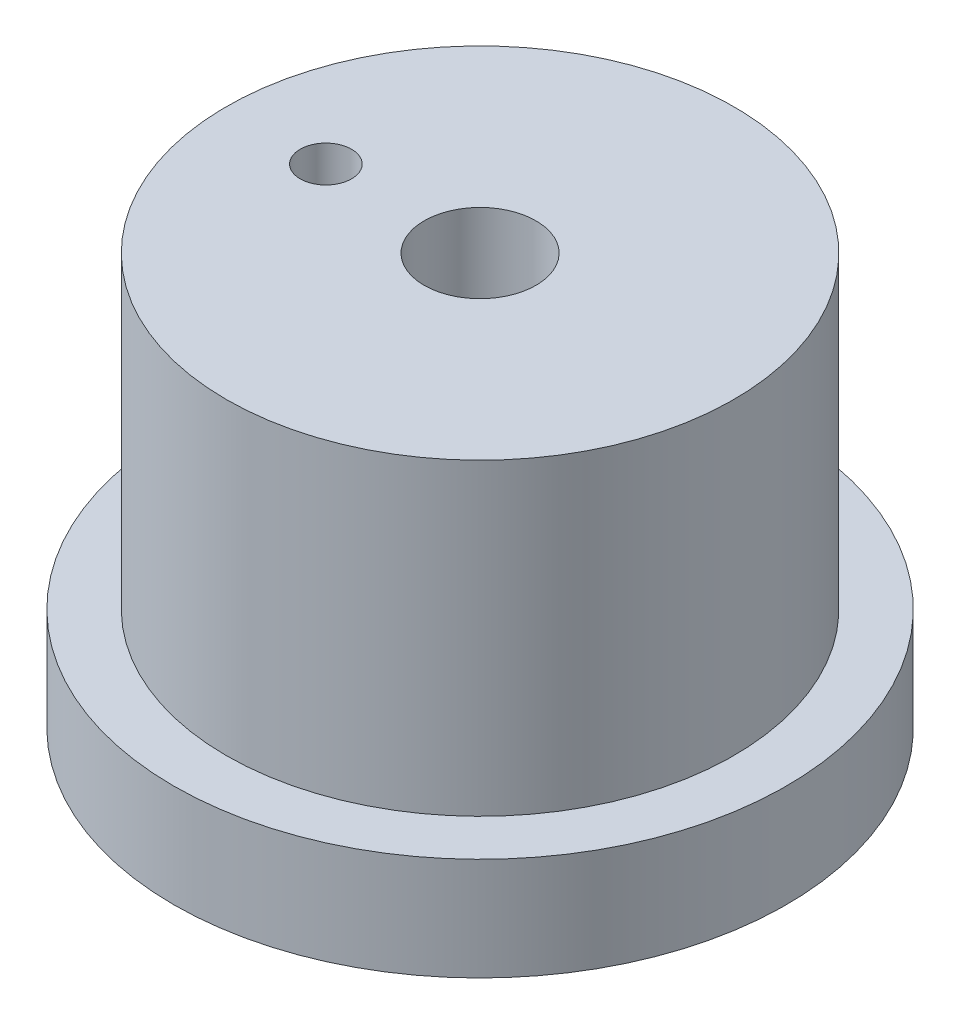
SolidWorks part; units mm, degrees
material "Stainless Steel"
ref_plane "Front Plane" through (0, 0, 0) normal (0, 0, 1) x (1, 0, 0)
ref_plane "Top Plane" through (0, 0, 0) normal (0, 1, 0) x (1, 0, 0)
ref_plane "Right Plane" through (0, 0, 0) normal (1, 0, 0) x (0, 0, -1)
sketch "Sketch1" plane through (0, 0, 0) normal (0, 1, 0) x (1, 0, 0)
  circle A0 centre (0, 0) radius 9.4615
  dimension "D1" = 18.923
extrude "Extrude1" add sketch "Sketch1" along normal blind 3.175
sketch "Sketch2" plane through (0, 3.175, 0) normal (0, 1, 0) x (1, 0, 0)
  circle A0 centre (0, 0) radius 7.8359
  dimension "D1" = 15.6718
extrude "Extrude2" add sketch "Sketch2" along normal blind 9.525
sketch "Sketch3" plane through (0, 0, 0) normal (0, -1, 0) x (1, 0, 0)
  circle A0 centre (0, 0) radius 7.4295
  dimension "D1" = 14.859
extrude "Cut-Extrude1" cut sketch "Sketch3" against normal blind 0.635
sketch "Sketch4" plane through (0, 12.7, 0) normal (0, 1, 0) x (1, 0, 0)
  line L0 (-7.8359, 0) -> (7.8359, 0) construction
  line L1 (0, 7.8359) -> (0, -7.8359) construction
  circle A0 centre (0, 0) radius 7.8359 construction
  circle A1 centre (0, 0) radius 7.8359 construction
hole_wizard "#8-32 Tapped Hole1" positions "3DSketch1" profile "Sketch5" tap size "#8-32" standard "ANSI Inch" end condition up to next
sketch3d "3DSketch1"
  line L0 (-7.8359, 12.7, 0) -> (7.8359, 12.7, 0) construction
  line L1 (0, 12.7, -7.8359) -> (0, 12.7, 7.8359) construction
  point P0 (0, 12.7, 0)
sketch "Sketch5" plane through (0, 12.7, 0) normal (1, 0, 0) x (0, 0, 1)
  line L0 (0, 0) -> (0, 12.065)
  line L1 (0, 12.065) -> (1.7272, 12.065)
  line L2 (1.7272, 12.065) -> (1.7272, 0)
  line L5 (1.7272, 0) -> (0, 0)
  line L11 (0, -6.35) -> (0, 107.95) construction
  dimension "Thru Tap Drill Dia." = 3.4544
  dimension "Thru Tap Drill Depth" = 12.065
cosmetic thread "Hole Thread1" parameters "D2"=4.1656
hole_wizard "1/16 (0.0625) Diameter Hole1" positions "Sketch11" profile "Sketch12" hole size "1/16" standard "ANSI Inch" end condition through all
sketch "Sketch11" plane through (0, 12.7, 0) normal (0, 1, 0) x (1, 0, 0)
  point P0 (-4.7625, 0)
  dimension "D1" = 4.7625
sketch "Sketch12" plane through (-4.7625, 12.7, 0) normal (1, 0, 0) x (0, 0, 1)
  line L0 (0, 0) -> (0, 12.7)
  line L1 (0, 12.7) -> (0.7937, 12.7)
  line L2 (0.7937, 12.7) -> (0.7937, 0)
  line L5 (0.7937, 0) -> (0, 0)
  line L11 (0, -6.35) -> (0, 107.95) construction
  dimension "Thru Hole Dia." = 1.5875
  dimension "Thru Hole Depth" = 12.7
